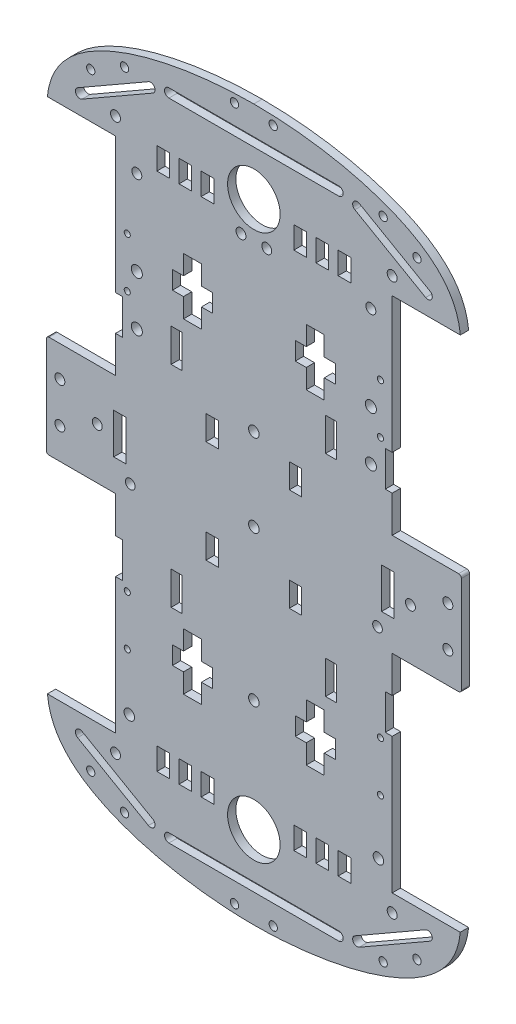
SolidWorks part; units mm, degrees
ref_plane "Plano frontal" through (0, 0, 0) normal (0, 0, 1) x (1, 0, 0)
ref_plane "Plano superior" through (0, 0, 0) normal (0, 1, 0) x (1, 0, 0)
ref_plane "Plano direito" through (0, 0, 0) normal (1, 0, 0) x (0, 0, -1)
sketch "Esboço1" plane through (0, 0, 0) normal (0, 0, 1) x (1, 0, 0)
  line L11 (30.699, 118.1902) -> (-30.699, 118.1902)
  line L12 (-30.699, 114.9902) -> (30.699, 114.9902)
  line L22 (-62.0964, 98.9462) -> (-36.5098, 113.6322)
  line L23 (-38.1027, 116.4076) -> (-63.6894, 101.7215)
  line L52 (62.8929, -100.3339) -> (37.3063, -115.0199) construction
  line L53 (62.0964, -98.9462) -> (36.5098, -113.6322)
  line L54 (63.6894, -101.7215) -> (38.1027, -116.4076)
  line L55 (-7.8851, -114.9902) -> (0, -128.5) construction
  line L56 (35.0506, -97.9605) -> (30.4506, -97.9605)
  line L57 (35.0506, -97.9605) -> (35.0506, -89.9605)
  line L58 (35.0506, -89.9605) -> (30.4506, -89.9605)
  line L59 (30.4506, -97.9605) -> (30.4506, -89.9605)
  line L60 (27.0506, -89.9605) -> (22.4506, -89.9605)
  line L61 (27.0506, -89.9605) -> (27.0506, -97.9605)
  line L62 (27.0506, -97.9605) -> (22.4506, -97.9605)
  line L63 (22.4506, -89.9605) -> (22.4506, -97.9605)
  line L64 (19.0506, -97.9605) -> (14.4506, -97.9605)
  line L65 (19.0506, -97.9605) -> (19.0506, -89.9605)
  line L66 (19.0506, -89.9605) -> (14.4506, -89.9605)
  line L67 (14.4506, -97.9605) -> (14.4506, -89.9605)
  line L68 (18.9416, -68.9834) -> (25.4416, -68.9834)
  line L69 (18.9416, -68.9834) -> (18.9416, -48.4834)
  line L70 (18.9416, -48.4834) -> (25.4416, -48.4834)
  line L71 (25.4416, -68.9834) -> (25.4416, -48.4834)
  line L72 (14.9747, -55.4834) -> (29.4289, -55.4834)
  line L73 (14.9747, -55.4834) -> (14.9747, -61.9834)
  line L74 (14.9747, -61.9834) -> (29.4289, -61.9834)
  line L75 (29.4289, -55.4834) -> (29.4289, -61.9834)
  line L76 (25.8965, -44.0251) -> (29.8965, -44.0251)
  line L77 (25.8965, -44.0251) -> (25.8965, -32.0251)
  line L78 (25.8965, -32.0251) -> (29.8965, -32.0251)
  line L79 (29.8965, -44.0251) -> (29.8965, -32.0251)
  line L80 (12.8104, -22.9668) -> (17.3104, -22.9668)
  line L81 (12.8104, -22.9668) -> (12.8104, -14.1027)
  line L112 (-50, 44.4469) -> (-47.5, 44.4469)
  line L113 (-47.5, 44.4469) -> (-47.5, 31.679)
  line L114 (-47.5, 31.679) -> (-50, 31.679)
  line L115 (-50, 31.679) -> (-50, 18.463)
  line L116 (-50, 18.463) -> (-74, 18.463)
  line L117 (-75, 17.463) -> (-75, -17.463)
  line L118 (-74, -18.463) -> (-50, -18.463)
  line L119 (-50, -18.463) -> (-50, -31.679)
  line L120 (-50, -31.679) -> (-47.5, -31.679)
  line L121 (-47.5, -31.679) -> (-47.5, -44.4469)
  line L122 (-47.5, -44.4469) -> (-50, -44.4469)
  line L123 (-50, -44.4469) -> (-50, -93.463)
  line L124 (-50, -93.463) -> (-74.6118, -93.463)
  line L125 (74.6118, -93.463) -> (50, -93.463)
  line L126 (50, -93.463) -> (50, -44.4469)
  line L127 (50, -44.4469) -> (47.5, -44.4469)
  line L128 (47.5, -44.4469) -> (47.5, -31.679)
  line L129 (47.5, -31.679) -> (50, -31.679)
  line L130 (50, -31.679) -> (50, -18.463)
  line L131 (50, -18.463) -> (74, -18.463)
  line L132 (75, -17.463) -> (75, 17.463)
  line L133 (74, 18.463) -> (50, 18.463)
  line L134 (50, 18.463) -> (50, 31.679)
  line L135 (50, 31.679) -> (47.5, 31.679)
  line L136 (47.5, 31.679) -> (47.5, 44.4469)
  line L137 (47.5, 44.4469) -> (50, 44.4469)
  line L138 (50, 44.4469) -> (50, 93.463)
  line L139 (50, 93.463) -> (74.6118, 93.463)
  line L140 (-74.6118, 93.463) -> (-50, 93.463)
  line L141 (-50, 93.463) -> (-50, 44.4469)
  line L142 (12.8104, -14.1027) -> (17.3104, -14.1027)
  line L143 (17.3104, -22.9668) -> (17.3104, -14.1027)
  line L144 (46.1416, -7.3) -> (50.6416, -7.3)
  line L145 (14.4506, -89.9605) -> (14.4506, -97.9605)
  line L146 (19.0506, -97.9605) -> (14.4506, -97.9605)
  line L147 (19.0506, -89.9605) -> (19.0506, -97.9605)
  line L148 (19.0506, -89.9605) -> (14.4506, -89.9605)
  line L149 (22.4506, -97.9605) -> (22.4506, -89.9605)
  line L150 (27.0506, -89.9605) -> (22.4506, -89.9605)
  line L151 (27.0506, -97.9605) -> (27.0506, -89.9605)
  line L152 (27.0506, -97.9605) -> (22.4506, -97.9605)
  line L153 (30.4506, -89.9605) -> (30.4506, -97.9605)
  line L154 (35.0506, -97.9605) -> (30.4506, -97.9605)
  line L155 (35.0506, -89.9605) -> (35.0506, -97.9605)
  line L156 (35.0506, -89.9605) -> (30.4506, -89.9605)
  line L157 (50.6416, 7.3) -> (50.6416, -7.3)
  line L158 (46.1416, -7.3) -> (50.6416, -7.3)
  line L159 (46.1416, 7.3) -> (46.1416, -7.3)
  line L160 (46.1416, 7.3) -> (50.6416, 7.3)
  line L161 (17.3104, 22.9668) -> (17.3104, 14.1027)
  line L162 (12.8104, 14.1027) -> (17.3104, 14.1027)
  line L163 (12.8104, 22.9668) -> (12.8104, 14.1027)
  line L164 (12.8104, 22.9668) -> (17.3104, 22.9668)
  line L165 (29.8965, 44.0251) -> (29.8965, 32.0251)
  line L166 (25.8965, 32.0251) -> (29.8965, 32.0251)
  line L167 (25.8965, 44.0251) -> (25.8965, 32.0251)
  line L168 (25.8965, 44.0251) -> (29.8965, 44.0251)
  line L169 (29.4289, 55.4834) -> (29.4289, 61.9834)
  line L170 (14.9747, 61.9834) -> (29.4289, 61.9834)
  line L171 (14.9747, 55.4834) -> (14.9747, 61.9834)
  line L172 (14.9747, 55.4834) -> (29.4289, 55.4834)
  line L173 (25.4416, 68.9834) -> (25.4416, 48.4834)
  line L174 (18.9416, 48.4834) -> (25.4416, 48.4834)
  line L175 (18.9416, 68.9834) -> (18.9416, 48.4834)
  line L176 (18.9416, 68.9834) -> (25.4416, 68.9834)
  line L177 (14.4506, 97.9605) -> (14.4506, 89.9605)
  line L178 (19.0506, 89.9605) -> (14.4506, 89.9605)
  line L179 (19.0506, 97.9605) -> (19.0506, 89.9605)
  line L180 (19.0506, 97.9605) -> (14.4506, 97.9605)
  line L181 (22.4506, 89.9605) -> (22.4506, 97.9605)
  line L182 (27.0506, 97.9605) -> (22.4506, 97.9605)
  line L183 (27.0506, 89.9605) -> (27.0506, 97.9605)
  line L184 (27.0506, 89.9605) -> (22.4506, 89.9605)
  line L185 (30.4506, 97.9605) -> (30.4506, 89.9605)
  line L186 (35.0506, 89.9605) -> (30.4506, 89.9605)
  line L187 (35.0506, 97.9605) -> (35.0506, 89.9605)
  line L188 (35.0506, 97.9605) -> (30.4506, 97.9605)
  line L189 (50, 93.463) -> (50, 44.4469)
  line L190 (74.6118, 93.463) -> (50, 93.463)
  line L191 (50, -93.463) -> (74.6118, -93.463)
  line L192 (50, -44.4469) -> (50, -93.463)
  line L193 (47.5, -44.4469) -> (50, -44.4469)
  line L194 (47.5, -31.679) -> (47.5, -44.4469)
  line L195 (50, -31.679) -> (47.5, -31.679)
  line L196 (50, -18.463) -> (50, -31.679)
  line L197 (74, -18.463) -> (50, -18.463)
  line L198 (75, 17.463) -> (75, -17.463)
  line L199 (50, 18.463) -> (74, 18.463)
  line L200 (50, 31.679) -> (50, 18.463)
  line L201 (47.5, 31.679) -> (50, 31.679)
  line L202 (47.5, 44.4469) -> (47.5, 31.679)
  line L203 (50, 44.4469) -> (47.5, 44.4469)
  line L204 (38.1027, 116.4076) -> (63.6894, 101.7215)
  line L205 (62.0964, 98.9462) -> (36.5098, 113.6322)
  line L839 (-62.8929, -100.3339) -> (-37.3063, -115.0199) construction
  line L840 (-35.0506, 97.9605) -> (-30.4506, 97.9605)
  line L841 (-35.0506, 97.9605) -> (-35.0506, 89.9605)
  line L842 (-35.0506, 89.9605) -> (-30.4506, 89.9605)
  line L843 (-30.4506, 97.9605) -> (-30.4506, 89.9605)
  line L844 (-27.0506, 89.9605) -> (-22.4506, 89.9605)
  line L845 (-27.0506, 89.9605) -> (-27.0506, 97.9605)
  line L846 (-27.0506, 97.9605) -> (-22.4506, 97.9605)
  line L847 (-22.4506, 89.9605) -> (-22.4506, 97.9605)
  line L848 (-19.0506, 97.9605) -> (-14.4506, 97.9605)
  line L849 (-19.0506, 97.9605) -> (-19.0506, 89.9605)
  line L850 (-19.0506, 89.9605) -> (-14.4506, 89.9605)
  line L851 (-14.4506, 97.9605) -> (-14.4506, 89.9605)
  line L852 (-18.9416, 68.9834) -> (-25.4416, 68.9834)
  line L853 (-18.9416, 68.9834) -> (-18.9416, 48.4834)
  line L854 (-18.9416, 48.4834) -> (-25.4416, 48.4834)
  line L855 (-25.4416, 68.9834) -> (-25.4416, 48.4834)
  line L856 (-14.9747, 55.4834) -> (-29.4289, 55.4834)
  line L857 (-14.9747, 55.4834) -> (-14.9747, 61.9834)
  line L858 (-14.9747, 61.9834) -> (-29.4289, 61.9834)
  line L859 (-29.4289, 55.4834) -> (-29.4289, 61.9834)
  line L860 (-25.8965, 44.0251) -> (-29.8965, 44.0251)
  line L861 (-25.8965, 44.0251) -> (-25.8965, 32.0251)
  line L862 (-25.8965, 32.0251) -> (-29.8965, 32.0251)
  line L863 (-29.8965, 44.0251) -> (-29.8965, 32.0251)
  line L864 (-12.8104, 22.9668) -> (-17.3104, 22.9668)
  line L865 (-12.8104, 22.9668) -> (-12.8104, 14.1027)
  line L866 (-12.8104, 14.1027) -> (-17.3104, 14.1027)
  line L867 (-17.3104, 22.9668) -> (-17.3104, 14.1027)
  line L868 (-46.1416, 7.3) -> (-50.6416, 7.3)
  line L869 (-46.1416, 7.3) -> (-46.1416, -7.3)
  line L870 (-46.1416, -7.3) -> (-50.6416, -7.3)
  line L871 (-50.6416, 7.3) -> (-50.6416, -7.3)
  line L872 (-35.0506, -89.9605) -> (-30.4506, -89.9605)
  line L873 (-35.0506, -89.9605) -> (-35.0506, -97.9605)
  line L874 (-35.0506, -97.9605) -> (-30.4506, -97.9605)
  line L875 (-30.4506, -89.9605) -> (-30.4506, -97.9605)
  line L876 (-27.0506, -97.9605) -> (-22.4506, -97.9605)
  line L877 (-27.0506, -97.9605) -> (-27.0506, -89.9605)
  line L878 (-27.0506, -89.9605) -> (-22.4506, -89.9605)
  line L879 (-22.4506, -97.9605) -> (-22.4506, -89.9605)
  line L880 (-19.0506, -89.9605) -> (-14.4506, -89.9605)
  line L881 (-19.0506, -89.9605) -> (-19.0506, -97.9605)
  line L882 (-19.0506, -97.9605) -> (-14.4506, -97.9605)
  line L883 (-14.4506, -89.9605) -> (-14.4506, -97.9605)
  line L884 (-62.0964, -98.9462) -> (-36.5098, -113.6322)
  line L885 (-63.6894, -101.7215) -> (-38.1027, -116.4076)
  line L887 (-30.699, -116.5902) -> (30.699, -116.5902) construction
  line L888 (-30.699, -114.9902) -> (30.699, -114.9902)
  line L889 (-30.699, -118.1902) -> (30.699, -118.1902)
  line L891 (-75, 0) -> (75, 0) construction
  line L894 (7.8851, -114.9902) -> (0, -128.5) construction
  line L895 (0, -128.5) -> (0, 128.5) construction
  line L896 (-46.1416, -7.3) -> (-50.6416, -7.3)
  line L897 (-17.3104, -22.9668) -> (-17.3104, -14.1027)
  line L898 (-12.8104, -14.1027) -> (-17.3104, -14.1027)
  line L899 (-12.8104, -22.9668) -> (-12.8104, -14.1027)
  line L900 (-12.8104, -22.9668) -> (-17.3104, -22.9668)
  line L901 (-29.8965, -44.0251) -> (-29.8965, -32.0251)
  line L902 (-25.8965, -32.0251) -> (-29.8965, -32.0251)
  line L903 (-25.8965, -44.0251) -> (-25.8965, -32.0251)
  line L904 (-25.8965, -44.0251) -> (-29.8965, -44.0251)
  line L905 (-29.4289, -55.4834) -> (-29.4289, -61.9834)
  line L906 (-14.9747, -61.9834) -> (-29.4289, -61.9834)
  line L907 (-14.9747, -55.4834) -> (-14.9747, -61.9834)
  line L908 (-14.9747, -55.4834) -> (-29.4289, -55.4834)
  line L909 (-25.4416, -68.9834) -> (-25.4416, -48.4834)
  line L910 (-18.9416, -48.4834) -> (-25.4416, -48.4834)
  line L911 (-18.9416, -68.9834) -> (-18.9416, -48.4834)
  line L912 (-18.9416, -68.9834) -> (-25.4416, -68.9834)
  line L913 (-14.4506, -97.9605) -> (-14.4506, -89.9605)
  line L914 (-19.0506, -89.9605) -> (-14.4506, -89.9605)
  line L915 (-19.0506, -97.9605) -> (-19.0506, -89.9605)
  line L916 (-19.0506, -97.9605) -> (-14.4506, -97.9605)
  line L917 (-22.4506, -89.9605) -> (-22.4506, -97.9605)
  line L918 (-27.0506, -97.9605) -> (-22.4506, -97.9605)
  line L919 (-27.0506, -89.9605) -> (-27.0506, -97.9605)
  line L920 (-27.0506, -89.9605) -> (-22.4506, -89.9605)
  line L921 (-30.4506, -97.9605) -> (-30.4506, -89.9605)
  line L922 (-35.0506, -89.9605) -> (-30.4506, -89.9605)
  line L923 (-35.0506, -97.9605) -> (-35.0506, -89.9605)
  line L924 (-35.0506, -97.9605) -> (-30.4506, -97.9605)
  circle A7 centre (0, 98.6872) radius 9.5
  arc A9 (30.699, 114.9902) -> (30.699, 118.1902) centre (30.699, 116.5902) ccw
  arc A10 (-30.699, 118.1902) -> (-30.699, 114.9902) centre (-30.699, 116.5902) ccw
  arc A16 (-63.6894, 101.7215) -> (-62.0964, 98.9462) centre (-62.8929, 100.3339) ccw
  arc A17 (-36.5098, 113.6322) -> (-38.1027, 116.4076) centre (-37.3063, 115.0199) ccw
  circle A19 centre (-46.7438, 116.6652) radius 1.5
  circle A22 centre (-7, 125.3171) radius 1.5
  circle A25 centre (-58.9562, 109.82) radius 1.5
  circle A28 centre (-49.9944, 99.7255) radius 1.8
  circle A31 centre (-42.2915, 85.6107) radius 1.8
  circle A34 centre (-42.2949, 54.918) radius 2
  circle A37 centre (-42.2969, 36.918) radius 2
  circle A40 centre (0, 25.9492) radius 1.9
  circle A43 centre (-4.6661, 85.6065) radius 1.8
  circle A46 centre (-70.1066, 7.3) radius 1.8
  circle A49 centre (-56.5934, 0) radius 1.8
  circle A52 centre (-44.6802, -12.7883) radius 1.75
  circle A55 centre (-70.1066, -7.3) radius 1.8
  circle A58 centre (0, -3.8693) radius 1.9
  arc A62 (62.0964, -98.9462) -> (63.6894, -101.7215) centre (62.8929, -100.3339) cw
  arc A63 (38.1027, -116.4076) -> (36.5098, -113.6322) centre (37.3063, -115.0199) cw
  circle A64 centre (49.9944, -99.7255) radius 1.8
  circle A65 centre (45.0269, -85.1446) radius 1.9
  arc A70 (-74, 18.463) -> (-75, 17.463) centre (-74, 17.463) ccw
  arc A71 (-75, -17.463) -> (-74, -18.463) centre (-74, -17.463) ccw
  arc A72 (74, -18.463) -> (75, -17.463) centre (74, -17.463) ccw
  arc A73 (75, 17.463) -> (74, 18.463) centre (74, 17.463) ccw
  circle A74 centre (7, -125.3171) radius 1.5
  circle A75 centre (46.7438, -116.6652) radius 1.5
  circle A76 centre (58.9562, -109.82) radius 1.5
  arc A77 (75, -17.463) -> (74, -18.463) centre (74, -17.463) cw
  arc A78 (74, 18.463) -> (75, 17.463) centre (74, 17.463) cw
  circle A79 centre (70.1066, -7.3) radius 1.8
  circle A80 centre (44.6802, -12.7883) radius 1.75
  circle A81 centre (56.5934, 0) radius 1.8
  circle A82 centre (70.1066, 7.3) radius 1.8
  circle A83 centre (4.6661, 85.6065) radius 1.8
  circle A84 centre (42.2969, 36.918) radius 2
  circle A85 centre (42.2949, 54.918) radius 2
  circle A86 centre (42.2915, 85.6107) radius 1.8
  circle A87 centre (49.9944, 99.7255) radius 1.8
  circle A88 centre (58.9562, 109.82) radius 1.5
  circle A89 centre (7, 125.3171) radius 1.5
  circle A90 centre (46.7438, 116.6652) radius 1.5
  arc A91 (36.5098, 113.6322) -> (38.1027, 116.4076) centre (37.3063, 115.0199) cw
  arc A92 (63.6894, 101.7215) -> (62.0964, 98.9462) centre (62.8929, 100.3339) cw
  arc A93 (30.699, 118.1902) -> (30.699, 114.9902) centre (30.699, 116.5902) cw
  arc A297 (-62.0964, -98.9462) -> (-63.6894, -101.7215) centre (-62.8929, -100.3339) ccw
  arc A298 (-38.1027, -116.4076) -> (-36.5098, -113.6322) centre (-37.3063, -115.0199) ccw
  arc A299 (-30.699, -114.9902) -> (-30.699, -118.1902) centre (-30.699, -116.5902) ccw
  arc A300 (30.699, -118.1902) -> (30.699, -114.9902) centre (30.699, -116.5902) ccw
  circle A304 centre (-58.9562, -109.82) radius 1.5
  circle A307 centre (-46.7438, -116.6652) radius 1.5
  circle A310 centre (-7, -125.3171) radius 1.5
  circle A313 centre (0, -58.1845) radius 1.9
  circle A317 centre (-45.0269, -85.1446) radius 1.9
  circle A318 centre (0, -98.6872) radius 9.5
  circle A320 centre (-49.9944, -99.7255) radius 1.8
  spline S4 degree 5 poles (0, 128.5) (1.2535, 128.5) (3.7762, 128.4741) (7.6072, 128.3573) (12.8047, 128.0441) (19.4194, 127.3774) (26.1008, 126.4175) (32.7776, 125.1438) (39.3584, 123.5365) (45.7287, 121.5815) (51.7542, 119.2734) (57.294, 116.6114) (62.2128, 113.5981) (66.3948, 110.2389) (69.7607, 106.542) (72.2834, 102.5191) (73.6281, 99.0493) (74.2639, 96.3093) (74.5233, 94.4219) (74.6118, 93.463) knots 0 0 0 0 0 0 0.066667 0.133333 0.2 0.266667 0.333333 0.4 0.466667 0.533333 0.6 0.666667 0.733333 0.8 0.866667 0.933333 1 1 1 1 1 1 weights 1 1 1 1 1 1 1 1 1 1 1 1 1 1 1 1 1 1 1 1
  spline S5 degree 5 poles (74.6118, -93.463) (74.5233, -94.4219) (74.2639, -96.3093) (73.6281, -99.0493) (72.2834, -102.5191) (69.7607, -106.542) (66.3948, -110.2389) (62.2128, -113.5981) (57.294, -116.6114) (51.7542, -119.2734) (45.7287, -121.5815) (39.3584, -123.5365) (32.7776, -125.1438) (26.1008, -126.4175) (19.4194, -127.3774) (12.8047, -128.0441) (7.6072, -128.3573) (3.7762, -128.4741) (1.2535, -128.5) (0, -128.5) knots 0 0 0 0 0 0 0.066667 0.133333 0.2 0.266667 0.333333 0.4 0.466667 0.533333 0.6 0.666667 0.733333 0.8 0.866667 0.933333 1 1 1 1 1 1 weights 1 1 1 1 1 1 1 1 1 1 1 1 1 1 1 1 1 1 1 1
  spline S12 degree 5 poles (-74.6118, -93.463) (-74.5233, -94.4219) (-74.2639, -96.3093) (-73.6281, -99.0493) (-72.2834, -102.5191) (-69.7607, -106.542) (-66.3948, -110.2389) (-62.2128, -113.5981) (-57.294, -116.6114) (-51.7542, -119.2734) (-45.7287, -121.5815) (-39.3584, -123.5365) (-32.7776, -125.1438) (-26.1008, -126.4175) (-19.4194, -127.3774) (-12.8047, -128.0441) (-7.6072, -128.3573) (-3.7762, -128.4741) (-1.2535, -128.5) (0, -128.5) knots 0 0 0 0 0 0 0.066667 0.133333 0.2 0.266667 0.333333 0.4 0.466667 0.533333 0.6 0.666667 0.733333 0.8 0.866667 0.933333 1 1 1 1 1 1 weights 1 1 1 1 1 1 1 1 1 1 1 1 1 1 1 1 1 1 1 1
  spline S13 degree 5 poles (0, -128.5) (1.2535, -128.5) (3.7762, -128.4741) (7.6072, -128.3573) (12.8047, -128.0441) (19.4194, -127.3774) (26.1008, -126.4175) (32.7776, -125.1438) (39.3584, -123.5365) (45.7287, -121.5815) (51.7542, -119.2734) (57.294, -116.6114) (62.2128, -113.5981) (66.3948, -110.2389) (69.7607, -106.542) (72.2834, -102.5191) (73.6281, -99.0493) (74.2639, -96.3093) (74.5233, -94.4219) (74.6118, -93.463) knots 0 0 0 0 0 0 0.066667 0.133333 0.2 0.266667 0.333333 0.4 0.466667 0.533333 0.6 0.666667 0.733333 0.8 0.866667 0.933333 1 1 1 1 1 1 weights 1 1 1 1 1 1 1 1 1 1 1 1 1 1 1 1 1 1 1 1
  spline S14 degree 5 poles (74.6118, 93.463) (74.5233, 94.4219) (74.2639, 96.3093) (73.6281, 99.0493) (72.2834, 102.5191) (69.7607, 106.542) (66.3948, 110.2389) (62.2128, 113.5981) (57.294, 116.6114) (51.7542, 119.2734) (45.7287, 121.5815) (39.3584, 123.5365) (32.7776, 125.1438) (26.1008, 126.4175) (19.4194, 127.3774) (12.8047, 128.0441) (7.6072, 128.3573) (3.7762, 128.4741) (1.2535, 128.5) (0, 128.5) knots 0 0 0 0 0 0 0.066667 0.133333 0.2 0.266667 0.333333 0.4 0.466667 0.533333 0.6 0.666667 0.733333 0.8 0.866667 0.933333 1 1 1 1 1 1 weights 1 1 1 1 1 1 1 1 1 1 1 1 1 1 1 1 1 1 1 1
  spline S15 degree 5 poles (0, 128.5) (-1.2535, 128.5) (-3.7762, 128.4741) (-7.6072, 128.3573) (-12.8047, 128.0441) (-19.4194, 127.3774) (-26.1008, 126.4175) (-32.7776, 125.1438) (-39.3584, 123.5365) (-45.7287, 121.5815) (-51.7542, 119.2734) (-57.294, 116.6114) (-62.2128, 113.5981) (-66.3948, 110.2389) (-69.7607, 106.542) (-72.2834, 102.5191) (-73.6281, 99.0493) (-74.2639, 96.3093) (-74.5233, 94.4219) (-74.6118, 93.463) knots 0 0 0 0 0 0 0.066667 0.133333 0.2 0.266667 0.333333 0.4 0.466667 0.533333 0.6 0.666667 0.733333 0.8 0.866667 0.933333 1 1 1 1 1 1 weights 1 1 1 1 1 1 1 1 1 1 1 1 1 1 1 1 1 1 1 1
  point P45 (-50.0996, -107.6769)
  point P54 (0, -116.5902)
  point P109 (50.0996, -107.6769)
extrude "Ressalto-extrusão1" add sketch "Esboço1" along normal blind 3 contours S4 S15 L140 L141 L112 L113 L114 L115 L116 A70 L117 A71 L118 L119 L120 L121 L122 L123 L124 S12 S5 L125 L126 L127 L128 L129 L130 L131 A72 L132 A73 L133 L134 L135 L136 L137 L138 L139 A318 A317 A313 A310 A307 A304
sketch "Esboço2" plane through (0, 0, 3) normal (0, 0, 1) x (1, 0, 0)
  line L0 (-50, 93.463) -> (-50, 44.4469) construction
  line L1 (-75, 0) -> (75, 0) construction
  line L2 (-75, 17.463) -> (-75, -17.463) construction
  line L3 (75, -17.463) -> (75, 17.463) construction
  line L4 (0, 128.5) -> (0, -128.5) construction
  circle A0 centre (-45.75, 47) radius 1.1
  circle A1 centre (-45.75, 65) radius 1.1
  circle A2 centre (-45.75, -65) radius 1.1
  circle A3 centre (-45.75, -47) radius 1.1
  circle A4 centre (45.75, -47) radius 1.1
  circle A5 centre (45.75, -65) radius 1.1
  circle A6 centre (45.75, 65) radius 1.1
  circle A7 centre (45.75, 47) radius 1.1
  dimension "D1" = 2.2
  dimension "D2" = 4.25
  dimension "D3" = 18
  dimension "D4" = 4.25
  dimension "D5" = 47
extrude "Corte-extrusão1" cut sketch "Esboço2" against normal through all
